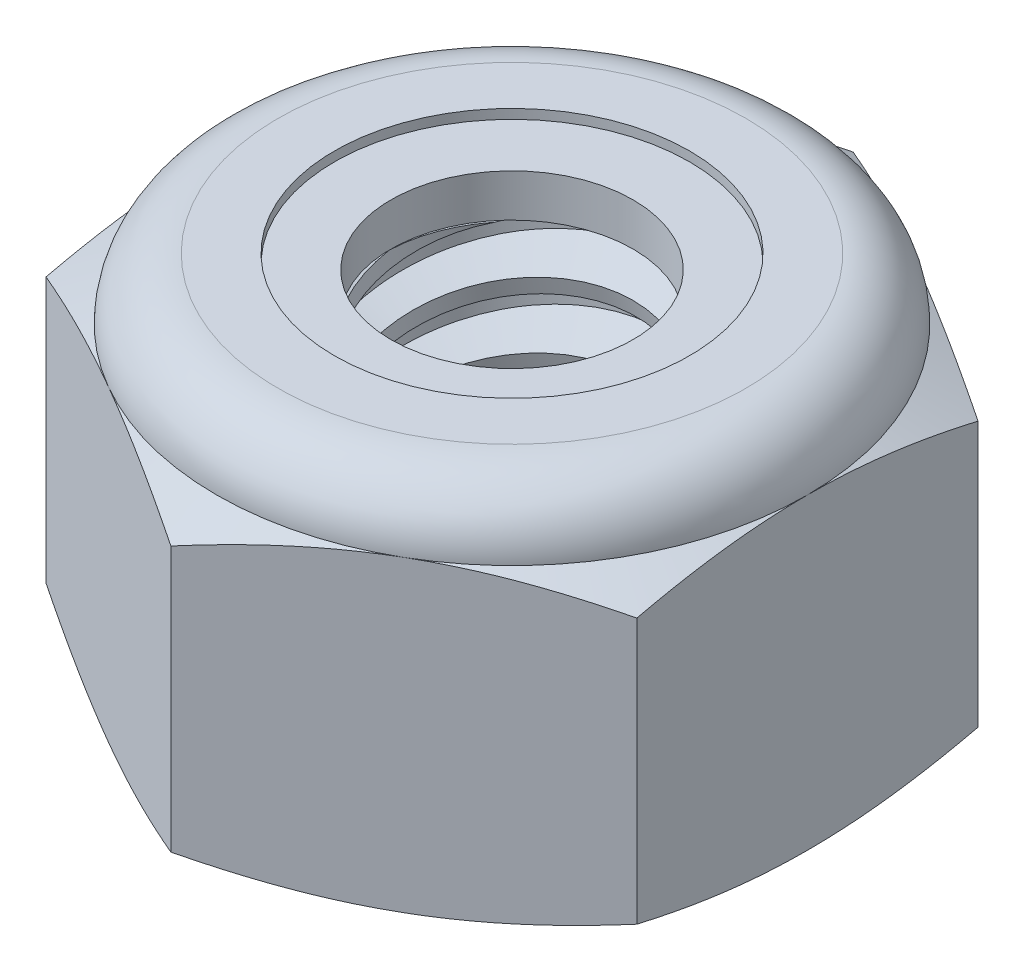
SolidWorks part; units mm, degrees
material "Cast Alloy Steel"
ref_plane "Front" through (0, 0, 0) normal (0, 0, 1) x (1, 0, 0)
ref_plane "Top" through (0, 0, 0) normal (0, 1, 0) x (1, 0, 0)
ref_plane "Right" through (0, 0, 0) normal (1, 0, 0) x (0, 0, -1)
sketch "Sketch1" plane through (0, 0, 0) normal (0, 1, 0) x (1, 0, 0)
  line L1 (0, 5.4993) -> (-4.7625, 2.7496)
  line L2 (-4.7625, 2.7496) -> (-4.7625, -2.7496)
  line L3 (-4.7625, -2.7496) -> (0, -5.4993)
  line L4 (0, -5.4993) -> (4.7625, -2.7496)
  line L5 (4.7625, -2.7496) -> (4.7625, 2.7496)
  line L6 (4.7625, 2.7496) -> (0, 5.4993)
  circle A0 centre (0, 0) radius 4.7625 construction
  dimension "Hex Flats" = 9.525
extrude "Extrude1" add sketch "Sketch1" along normal blind 5.9531
sketch "Sketch2" plane through (0, 0, 0) normal (1, 0, 0) x (0, 0, -1)
  line L0 (-2.413, 0) -> (-2.413, 5.9531) construction
  line L1 (0, 0) -> (2.413, 0)
  line L2 (0, 0) -> (0, 5.9531)
  line L3 (0, 5.9531) -> (2.413, 5.9531)
  line L4 (2.413, 0) -> (2.413, 5.9531)
  line L5 (-2.7496, 5.9531) -> (2.7496, 5.9531) construction
  line L7 (0, -2.413) -> (0, 0) construction
  dimension "Thread Dia" = 4.826
revolve "Revolve1" add sketch "Sketch2" angle 360 about L7
sketch "Sketch3" plane through (0, 0, 0) normal (1, 0, 0) x (0, 0, -1)
  line L0 (2.413, 5.9531) -> (-2.413, 5.9531) construction
  line L1 (-2.413, 5.9531) -> (-2.413, 4.8948) construction
  line L2 (-2.413, 4.8948) -> (2.413, 5.9531) construction
  line L3 (2.413, 5.9531) -> (2.4413, 5.8239) construction
  line L4 (2.4413, 5.8239) -> (2.6397, 4.9194)
  line L5 (2.6397, 4.9194) -> (2.0093, 5.1197)
  line L6 (2.0093, 5.1197) -> (1.9526, 5.3781)
  line L7 (1.9526, 5.3781) -> (2.4413, 5.8239)
  line L8 (1.981, 5.2489) -> (2.5405, 5.3716) construction
  line L9 (2.413, 5.9531) -> (2.413, 5.3437) construction
  line L10 (2.413, 5.3437) -> (-2.413, 4.2853) construction
  line L11 (-2.413, 4.2853) -> (-2.413, 4.8948) construction
  line L12 (-0.2497, 5.9531) -> (0.2497, 3.6759) construction
  line L13 (-2.413, 0) -> (-2.413, 5.9531) construction
  line L14 (0, 5.9531) -> (2.413, 5.9531) construction
  line L15 (2.413, 0) -> (2.413, 5.9531) construction
  point P13 (0, 4.8145)
  dimension "D1" = 0.1323
  dimension "D2" = 0.2646
  dimension "Thread Pitch" = 1.0583
  dimension "D4" = 60
  dimension "D5" = 1.0583
revolve "Cut-Revolve1" cut sketch "Sketch3" angle 360 about L12
pattern_linear "LPattern1" count 6 spacing 1.0583 along (0, -1, 0) count 2 spacing 1.0583 along (0, 1, 0) of "Cut-Revolve1"
sketch "Sketch4" plane through (0, 0, 0) normal (1, 0, 0) x (0, 0, -1)
  line L0 (0, 5.9531) -> (2.413, 5.9531)
  line L1 (2.413, 5.9531) -> (1.9526, 5.7385)
  line L2 (1.9526, 5.7385) -> (1.9526, 0.2147)
  line L3 (1.9526, 0.2147) -> (2.413, 0)
  line L4 (2.413, 0) -> (0, 0)
  line L5 (0, 0) -> (0, 5.9531)
  line L6 (2.413, 0) -> (2.413, 5.9531) construction
  line L7 (0, 5.9531) -> (2.413, 5.9531) construction
  line L8 (0, 0) -> (2.413, 0) construction
  line L9 (0, 0) -> (0, 5.9531) construction
  line L10 (0, 5.9531) -> (0, 6.4611) construction
  dimension "D1" = 25
revolve "Cut-Revolve2" cut sketch "Sketch4" angle 360 about L10
combine bodies "Combine1" operation type subtract main body 112 bodies to subtract 111
sketch "Sketch5" plane through (0, 0, 0) normal (1, 0, 0) x (0, 0, -1)
  line L0 (0, 0) -> (4.7625, 0)
  line L1 (4.7625, 0) -> (5.4993, 0.3436)
  line L2 (5.4993, 0.3436) -> (5.4993, 4.6174)
  line L3 (5.4993, 4.6174) -> (4.7625, 4.9609)
  line L4 (3.7703, 5.9531) -> (3.7703, 7.2231)
  line L5 (3.7703, 7.2231) -> (6.7693, 7.2231)
  line L6 (6.7693, 7.2231) -> (6.7693, -1.27)
  line L7 (6.7693, -1.27) -> (0, -1.27)
  line L8 (0, -1.27) -> (0, 0)
  line L9 (4.7625, 4.9609) -> (4.7625, 0) construction
  line L10 (0, 0) -> (2.413, 0) construction
  line L13 (5.4993, 2.4805) -> (6.7693, 2.4805) construction
  line L14 (5.4993, 5.9531) -> (5.4993, 0) construction
  line L15 (0, 0) -> (0, 7.2231) construction
  line L20 (0, 7.2231) -> (3.7703, 7.2231) construction
  line L22 (0, 5.9531) -> (2.413, 5.9531) construction
  arc A0 (4.7625, 4.9609) -> (3.7703, 5.9531) centre (3.7703, 4.9609) ccw
  dimension "D1" = 25
  dimension "D2" = 1.27
  dimension "D3" = 5.9531
  dimension "D4" = 0.9922
revolve "Cut-Revolve3" cut sketch "Sketch5" angle 360 about L15
sketch "Sketch6" plane through (0, 0, 0) normal (1, 0, 0) x (0, 0, -1)
  line L0 (0, 4.9609) -> (4.6101, 4.9609)
  line L1 (3.7703, 5.8007) -> (2.8615, 5.8007)
  line L2 (0, 7.2231) -> (0, 4.9609)
  line L3 (2.8615, 7.2231) -> (0, 7.2231)
  line L4 (0, 7.2231) -> (3.7703, 7.2231) construction
  line L5 (0, 0) -> (0, 7.2231) construction
  line L6 (0, 7.2231) -> (0, 44.323) construction
  line L7 (2.8615, 5.8007) -> (2.8615, 7.2231)
  line L8 (3.7703, 5.9531) -> (3.7703, 5.8007) construction
  line L9 (2.8615, 5.8007) -> (1.9526, 5.8007) construction
  line L10 (1.9526, 5.8007) -> (1.9526, 5.7385) construction
  arc A0 (4.6101, 4.9609) -> (3.7703, 5.8007) centre (3.7703, 4.9609) ccw
  arc A1 (4.7625, 4.9609) -> (3.7703, 5.9531) centre (3.7703, 4.9609) ccw construction
  dimension "D1" = 0.1524
revolve "Cut-Revolve4" cut sketch "Sketch6" angle 360 about L6
sketch "Sketch7" plane through (0, 0, 0) normal (1, 0, 0) x (0, 0, -1)
  line L0 (1.9526, 5.0371) -> (4.5301, 5.0371)
  line L1 (3.7703, 5.7245) -> (1.9526, 5.7245)
  line L2 (1.9526, 5.7245) -> (1.9526, 5.0371)
  line L3 (1.9526, 5.0371) -> (0, 5.0371) construction
  line L4 (0, 5.0371) -> (0, 5.7245) construction
  line L5 (0, 5.7245) -> (1.9526, 5.7245) construction
  line L6 (1.9526, 5.0371) -> (1.9526, 4.9609) construction
  line L7 (0, 4.9609) -> (4.6101, 4.9609) construction
  line L8 (3.7703, 5.7245) -> (3.7703, 5.8007) construction
  arc A0 (4.5301, 5.0371) -> (3.7703, 5.7245) centre (3.7703, 4.9609) ccw
  arc A2 (4.6101, 4.9609) -> (3.7703, 5.8007) centre (3.7703, 4.9609) ccw construction
  dimension "D1" = 0.0762
revolve "Revolve2" add sketch "Sketch7" angle 360 about L4
equation "\"D1@Sketch3\"=\"Thread Pitch@Sketch3\"/8"
equation "\"D2@Sketch3\"=\"Thread Pitch@Sketch3\"/4"
equation "\"D5@Sketch3\"=\"Thread Pitch@Sketch3\""
equation "\"D4@LPattern1\"=\"Thread Pitch@Sketch3\""
equation "\"D3@LPattern1\"=\"Thread Pitch@Sketch3\""
equation "\"D1@LPattern1\"=\"Height@Extrude1\"/\"Thread Pitch@Sketch3\""
equation "\"D4@Sketch5\"=\"Height@Extrude1\"/6"
